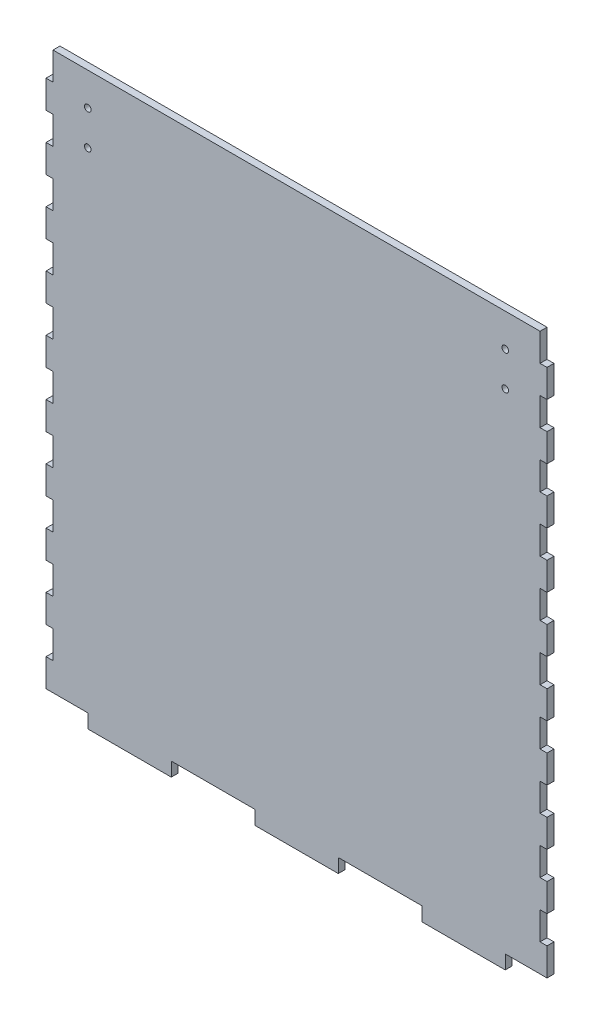
SolidWorks part; units mm, degrees
material "Acrylic (Medium-high impact)"
ref_plane "Front Plane" through (0, 0, 0) normal (0, 0, 1) x (1, 0, 0)
ref_plane "Top Plane" through (0, 0, 0) normal (0, 1, 0) x (1, 0, 0)
ref_plane "Right Plane" through (0, 0, 0) normal (1, 0, 0) x (0, 0, -1)
sketch "Sketch1" plane through (0, 0, 0) normal (0, 0, 1) x (1, 0, 0)
  line L0 (-114.3, 114.3) -> (-111.125, 114.3)
  line L1 (-114.3, 127) -> (114.3, 127)
  line L2 (-114.3, 127) -> (-114.3, -127)
  line L3 (-114.3, -127) -> (114.3, -127)
  line L4 (114.3, 127) -> (114.3, -127)
  line L5 (-114.3, 127) -> (-111.125, 127)
  line L6 (-114.3, 127) -> (-114.3, 114.3)
  line L7 (-114.3, 114.3) -> (-111.125, 114.3)
  line L8 (-111.125, 127) -> (-111.125, 114.3)
  line L9 (-114.3, 114.3) -> (-114.3, 101.6)
  line L10 (-114.3, 101.6) -> (-111.125, 101.6)
  line L11 (-111.125, 114.3) -> (-111.125, 101.6)
  line L12 (-114.3, 101.6) -> (-111.125, 101.6)
  line L13 (-114.3, 101.6) -> (-114.3, 88.9)
  line L14 (-114.3, 88.9) -> (-111.125, 88.9)
  line L15 (-111.125, 101.6) -> (-111.125, 88.9)
  line L16 (-114.3, 88.9) -> (-111.125, 88.9)
  line L17 (-114.3, 88.9) -> (-114.3, 76.2)
  line L18 (-114.3, 76.2) -> (-111.125, 76.2)
  line L19 (-111.125, 88.9) -> (-111.125, 76.2)
  line L20 (-114.3, 76.2) -> (-111.125, 76.2)
  line L21 (-114.3, 76.2) -> (-114.3, 63.5)
  line L22 (-114.3, 63.5) -> (-111.125, 63.5)
  line L23 (-111.125, 76.2) -> (-111.125, 63.5)
  line L24 (-114.3, 63.5) -> (-111.125, 63.5)
  line L25 (-114.3, 63.5) -> (-114.3, 50.8)
  line L26 (-114.3, 50.8) -> (-111.125, 50.8)
  line L27 (-111.125, 63.5) -> (-111.125, 50.8)
  line L28 (-114.3, 50.8) -> (-111.125, 50.8)
  line L29 (-114.3, 50.8) -> (-114.3, 38.1)
  line L30 (-114.3, 38.1) -> (-111.125, 38.1)
  line L31 (-111.125, 50.8) -> (-111.125, 38.1)
  line L32 (-114.3, 38.1) -> (-111.125, 38.1)
  line L33 (-114.3, 38.1) -> (-114.3, 25.4)
  line L34 (-114.3, 25.4) -> (-111.125, 25.4)
  line L35 (-111.125, 38.1) -> (-111.125, 25.4)
  line L36 (-114.3, 25.4) -> (-111.125, 25.4)
  line L37 (-114.3, 25.4) -> (-114.3, 12.7)
  line L38 (-114.3, 12.7) -> (-111.125, 12.7)
  line L39 (-111.125, 25.4) -> (-111.125, 12.7)
  line L40 (-114.3, 12.7) -> (-111.125, 12.7)
  line L41 (-114.3, 12.7) -> (-114.3, 0)
  line L42 (-114.3, 0) -> (-111.125, 0)
  line L43 (-111.125, 12.7) -> (-111.125, 0)
  line L44 (-114.3, 0) -> (-111.125, 0)
  line L45 (-114.3, 0) -> (-114.3, -12.7)
  line L46 (-114.3, -12.7) -> (-111.125, -12.7)
  line L47 (-111.125, 0) -> (-111.125, -12.7)
  line L48 (-114.3, -12.7) -> (-111.125, -12.7)
  line L49 (-114.3, -12.7) -> (-114.3, -25.4)
  line L50 (-114.3, -25.4) -> (-111.125, -25.4)
  line L51 (-111.125, -12.7) -> (-111.125, -25.4)
  line L52 (-114.3, -25.4) -> (-111.125, -25.4)
  line L53 (-114.3, -25.4) -> (-114.3, -38.1)
  line L54 (-114.3, -38.1) -> (-111.125, -38.1)
  line L55 (-111.125, -25.4) -> (-111.125, -38.1)
  line L56 (-114.3, -38.1) -> (-111.125, -38.1)
  line L57 (-114.3, -38.1) -> (-114.3, -50.8)
  line L58 (-114.3, -50.8) -> (-111.125, -50.8)
  line L59 (-111.125, -38.1) -> (-111.125, -50.8)
  line L60 (-114.3, -50.8) -> (-111.125, -50.8)
  line L61 (-114.3, -50.8) -> (-114.3, -63.5)
  line L62 (-114.3, -63.5) -> (-111.125, -63.5)
  line L63 (-111.125, -50.8) -> (-111.125, -63.5)
  line L64 (-114.3, -63.5) -> (-111.125, -63.5)
  line L65 (-114.3, -63.5) -> (-114.3, -76.2)
  line L66 (-114.3, -76.2) -> (-111.125, -76.2)
  line L67 (-111.125, -63.5) -> (-111.125, -76.2)
  line L68 (-114.3, -76.2) -> (-111.125, -76.2)
  line L69 (-114.3, -76.2) -> (-114.3, -88.9)
  line L70 (-114.3, -88.9) -> (-111.125, -88.9)
  line L71 (-111.125, -76.2) -> (-111.125, -88.9)
  line L72 (-114.3, -88.9) -> (-111.125, -88.9)
  line L73 (-114.3, -88.9) -> (-114.3, -101.6)
  line L74 (-114.3, -101.6) -> (-111.125, -101.6)
  line L75 (-111.125, -88.9) -> (-111.125, -101.6)
  line L76 (-114.3, -101.6) -> (-111.125, -101.6)
  line L77 (-114.3, -101.6) -> (-114.3, -114.3)
  line L78 (-114.3, -114.3) -> (-111.125, -114.3)
  line L79 (-111.125, -101.6) -> (-111.125, -114.3)
  line L80 (-114.3, -114.3) -> (-111.125, -114.3)
  line L81 (-114.3, -114.3) -> (-114.3, -127)
  line L82 (-114.3, -127) -> (-111.125, -127)
  line L83 (-111.125, -114.3) -> (-111.125, -127)
  line L100 (0, 127) -> (0, -127) construction
  line L101 (114.3, 114.3) -> (111.125, 114.3)
  line L102 (114.3, 127) -> (111.125, 127)
  line L103 (114.3, 127) -> (114.3, 114.3)
  line L104 (114.3, 114.3) -> (111.125, 114.3)
  line L105 (111.125, 127) -> (111.125, 114.3)
  line L106 (114.3, 114.3) -> (114.3, 101.6)
  line L107 (114.3, 101.6) -> (111.125, 101.6)
  line L108 (111.125, 114.3) -> (111.125, 101.6)
  line L109 (114.3, 101.6) -> (111.125, 101.6)
  line L110 (114.3, 101.6) -> (114.3, 88.9)
  line L111 (114.3, 88.9) -> (111.125, 88.9)
  line L112 (111.125, 101.6) -> (111.125, 88.9)
  line L113 (114.3, 88.9) -> (111.125, 88.9)
  line L114 (114.3, 88.9) -> (114.3, 76.2)
  line L115 (114.3, 76.2) -> (111.125, 76.2)
  line L116 (111.125, 88.9) -> (111.125, 76.2)
  line L117 (114.3, 76.2) -> (111.125, 76.2)
  line L118 (114.3, 76.2) -> (114.3, 63.5)
  line L119 (114.3, 63.5) -> (111.125, 63.5)
  line L120 (111.125, 76.2) -> (111.125, 63.5)
  line L121 (114.3, 63.5) -> (111.125, 63.5)
  line L122 (114.3, 63.5) -> (114.3, 50.8)
  line L123 (114.3, 50.8) -> (111.125, 50.8)
  line L124 (111.125, 63.5) -> (111.125, 50.8)
  line L125 (114.3, 50.8) -> (111.125, 50.8)
  line L126 (114.3, 50.8) -> (114.3, 38.1)
  line L127 (114.3, 38.1) -> (111.125, 38.1)
  line L128 (111.125, 50.8) -> (111.125, 38.1)
  line L129 (114.3, 38.1) -> (111.125, 38.1)
  line L130 (114.3, 38.1) -> (114.3, 25.4)
  line L131 (114.3, 25.4) -> (111.125, 25.4)
  line L132 (111.125, 38.1) -> (111.125, 25.4)
  line L133 (114.3, 25.4) -> (111.125, 25.4)
  line L134 (114.3, 25.4) -> (114.3, 12.7)
  line L135 (114.3, 12.7) -> (111.125, 12.7)
  line L136 (111.125, 25.4) -> (111.125, 12.7)
  line L137 (114.3, 12.7) -> (111.125, 12.7)
  line L138 (114.3, 12.7) -> (114.3, 0)
  line L139 (114.3, 0) -> (111.125, 0)
  line L140 (111.125, 12.7) -> (111.125, 0)
  line L141 (114.3, 0) -> (111.125, 0)
  line L142 (114.3, 0) -> (114.3, -12.7)
  line L143 (114.3, -12.7) -> (111.125, -12.7)
  line L144 (111.125, 0) -> (111.125, -12.7)
  line L145 (114.3, -12.7) -> (111.125, -12.7)
  line L146 (114.3, -12.7) -> (114.3, -25.4)
  line L147 (114.3, -25.4) -> (111.125, -25.4)
  line L148 (111.125, -12.7) -> (111.125, -25.4)
  line L149 (114.3, -25.4) -> (111.125, -25.4)
  line L150 (114.3, -25.4) -> (114.3, -38.1)
  line L151 (114.3, -38.1) -> (111.125, -38.1)
  line L152 (111.125, -25.4) -> (111.125, -38.1)
  line L153 (114.3, -38.1) -> (111.125, -38.1)
  line L154 (114.3, -38.1) -> (114.3, -50.8)
  line L155 (114.3, -50.8) -> (111.125, -50.8)
  line L156 (111.125, -38.1) -> (111.125, -50.8)
  line L157 (114.3, -50.8) -> (111.125, -50.8)
  line L158 (114.3, -50.8) -> (114.3, -63.5)
  line L159 (114.3, -63.5) -> (111.125, -63.5)
  line L160 (111.125, -50.8) -> (111.125, -63.5)
  line L161 (114.3, -63.5) -> (111.125, -63.5)
  line L162 (114.3, -63.5) -> (114.3, -76.2)
  line L163 (114.3, -76.2) -> (111.125, -76.2)
  line L164 (111.125, -63.5) -> (111.125, -76.2)
  line L165 (114.3, -76.2) -> (111.125, -76.2)
  line L166 (114.3, -76.2) -> (114.3, -88.9)
  line L167 (114.3, -88.9) -> (111.125, -88.9)
  line L168 (111.125, -76.2) -> (111.125, -88.9)
  line L169 (114.3, -88.9) -> (111.125, -88.9)
  line L170 (114.3, -88.9) -> (114.3, -101.6)
  line L171 (114.3, -101.6) -> (111.125, -101.6)
  line L172 (111.125, -88.9) -> (111.125, -101.6)
  line L173 (114.3, -101.6) -> (111.125, -101.6)
  line L174 (114.3, -101.6) -> (114.3, -114.3)
  line L175 (114.3, -114.3) -> (111.125, -114.3)
  line L176 (111.125, -101.6) -> (111.125, -114.3)
  line L177 (114.3, -114.3) -> (111.125, -114.3)
  line L178 (114.3, -114.3) -> (114.3, -127)
  line L179 (114.3, -127) -> (111.125, -127)
  line L180 (111.125, -114.3) -> (111.125, -127)
  line L186 (95.25, -127) -> (95.25, -133.35)
  line L187 (95.25, -133.35) -> (57.15, -133.35)
  line L188 (57.15, -133.35) -> (57.15, -127)
  line L189 (57.15, -127) -> (95.25, -127)
  line L191 (-19.05, -127) -> (19.05, -127)
  line L192 (19.05, -127) -> (19.05, -133.35)
  line L193 (19.05, -133.35) -> (-19.05, -133.35)
  line L194 (-19.05, -133.35) -> (-19.05, -127)
  line L195 (-95.25, -127) -> (-57.15, -127)
  line L196 (-57.15, -127) -> (-57.15, -133.35)
  line L197 (-57.15, -133.35) -> (-95.25, -133.35)
  line L198 (-95.25, -133.35) -> (-95.25, -127)
  point P4 (0, 127)
  point P6 (-114.3, 0)
  dimension "D1" = 254
  dimension "D2" = 228.6
  dimension "D3" = 12.7
  dimension "D4" = 3.175
  dimension "D7" = 6.35
  dimension "D8" = 38.1
  dimension "D9" = 19.05
  dimension "D5" = 20
  dimension "D6" = 20
  dimension "D10" = 3
extrude "Boss-Extrude1" add sketch "Sketch1" along normal blind 3.175
sketch "Sketch2" plane through (0, 0, 3.175) normal (0, 0, 1) x (1, 0, 0)
  line L0 (-25.4, -88.9) -> (25.4, -88.9) construction
  line L1 (0, -85.725) -> (0, -114.3) construction
  line L2 (-15.5, -85.725) -> (15.5, -85.725)
  line L3 (-15.5, -85.725) -> (-15.5, -114.3)
  line L5 (95.25, -127) -> (114.3, -127) construction
  line L8 (-15.5, -114.3) -> (15.5, -114.3)
  line L9 (15.5, -85.725) -> (15.5, -114.3)
  line L12 (-114.3, -114.3) -> (-114.3, -127) construction
  circle A0 centre (-25.4, -88.9) radius 1.5
  circle A1 centre (25.4, -88.9) radius 1.5
  point P12 (0, -88.9)
  dimension "D1" = 3
  dimension "D2" = 50.8
  dimension "D3" = 31
  dimension "D4" = 25.4
  dimension "D5" = 28.575
  dimension "D6" = 12.7
  dimension "D7" = 114.3
extrude "Cut-Extrude1" [suppressed] cut sketch "Sketch2" against normal through all
sketch "Sketch3" plane through (0, 0, 0) normal (0, 0, -1) x (-1, 0, 0)
  line L0 (0, 127) -> (0, -133.35) construction
  line L1 (111.125, 127) -> (-111.125, 127) construction
  line L2 (-19.05, -133.35) -> (19.05, -133.35) construction
  line L3 (-114.3, 114.3) -> (-114.3, 101.6) construction
  circle A0 centre (-95.25, 112) radius 1.5
  circle A1 centre (-95.25, 96.25) radius 1.5
  circle A2 centre (95.25, 96.25) radius 1.5
  circle A3 centre (95.25, 112) radius 1.5
  dimension "D1" = 3
  dimension "D2" = 3
  dimension "D3" = 15.75
  dimension "D4" = 15
  dimension "D5" = 19.05
extrude "Cut-Extrude2" cut sketch "Sketch3" against normal up to surface (3.175 mm away) up to face at (0, -16.9793, 3.175)
